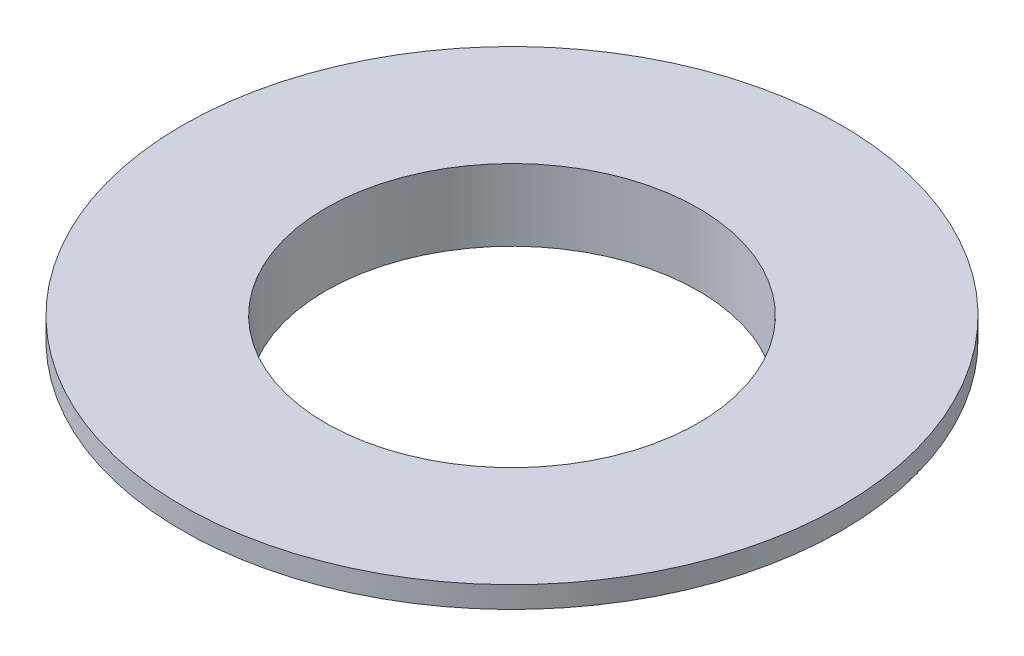
SolidWorks part; units mm, degrees
ref_plane "Front Plane" through (0, 0, 0) normal (0, 0, 1) x (1, 0, 0)
ref_plane "Top Plane" through (0, 0, 0) normal (0, 1, 0) x (1, 0, 0)
ref_plane "Right Plane" through (0, 0, 0) normal (1, 0, 0) x (0, 0, -1)
sketch "Sketch1" plane through (0, 0, 0) normal (0, 0, 1) x (1, 0, 0)
  line L0 (0, 0) -> (0, 10)
  line L1 (0, 10) -> (20, 10)
  line L2 (20, 10) -> (20, 7)
  line L3 (20, 7) -> (4, 7)
  line L4 (4, 7) -> (4, 0)
  line L5 (4, 0) -> (0, 0)
  line L6 (-26, 37.869) -> (-26, -14.493) construction
  dimension "D1" = 3
  dimension "D2" = 4
  dimension "D3" = 20
  dimension "D4" = 10
  dimension "D5" = 26
revolve "Revolve1" add sketch "Sketch1" angle 360 about L6
